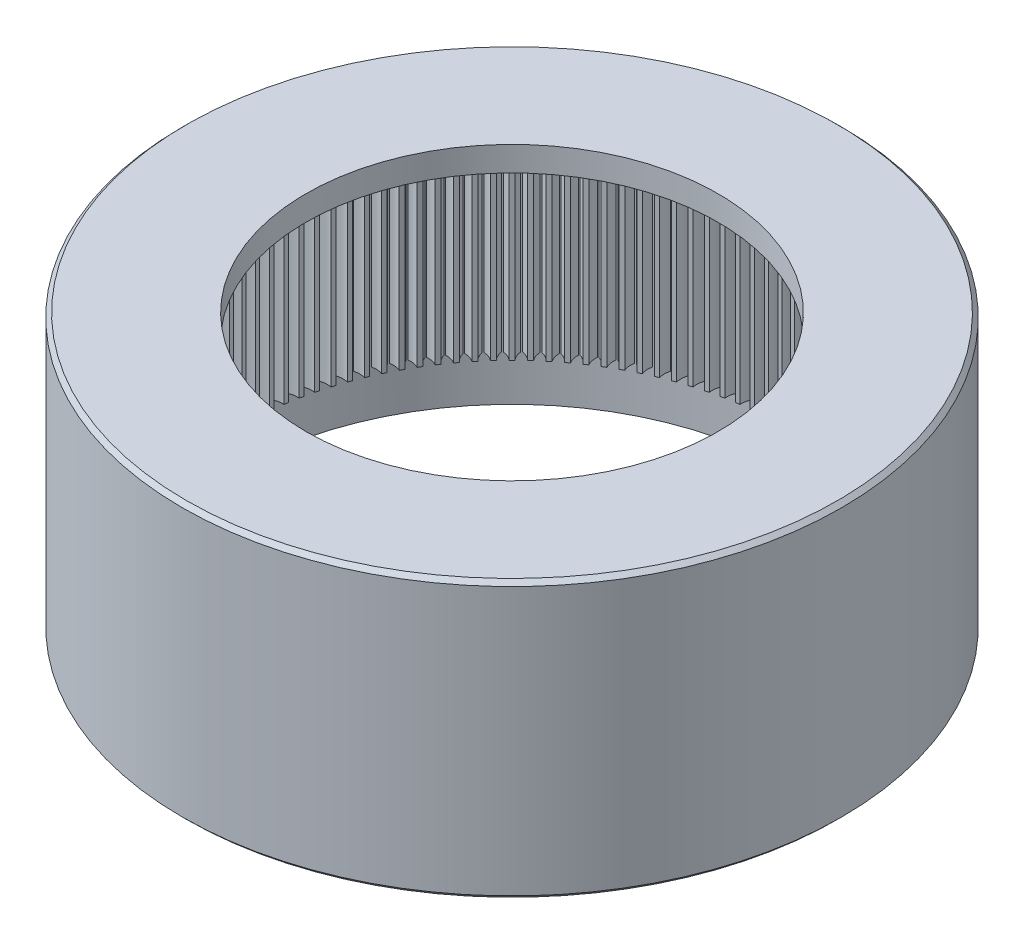
SolidWorks part; units mm, degrees
ref_plane "Front Plane" through (0, 0, 0) normal (0, 0, 1) x (1, 0, 0)
ref_plane "Top Plane" through (0, 0, 0) normal (0, 1, 0) x (1, 0, 0)
ref_plane "Right Plane" through (0, 0, 0) normal (1, 0, 0) x (0, 0, -1)
sketch "Sketch2" plane through (0, 0, 0) normal (0, 1, 0) x (1, 0, 0)
  circle A0 centre (0, 0) radius 75
  circle A1 centre (0, 0) radius 67.5
  dimension "D1" = 150
  dimension "D2" = 135
extrude "Boss-Extrude2" add sketch "Sketch2" along normal blind 51
sketch "Sketch3" plane through (0, 51, 0) normal (0, 1, 0) x (1, 0, 0)
  circle A0 centre (0, 0) radius 67.5 construction
  circle A1 centre (0, 0) radius 67.5
  circle A2 centre (0, 0) radius 65
  dimension "D1" = 130
extrude "Boss-Extrude3" add sketch "Sketch3" against normal blind 44
sketch "Sketch4" plane through (0, 51, 0) normal (0, 1, 0) x (1, 0, 0)
  circle A0 centre (0, 0) radius 67.5
  circle A1 centre (0, 0) radius 65
  dimension "D1" = 135
  dimension "D2" = 130
extrude "Cut-Extrude2" cut sketch "Sketch4" against normal blind 79
sketch "Sketch5" plane through (0, 51, 0) normal (0, 1, 0) x (1, 0, 0)
  line L0 (0, 0) -> (0, 80.4574) construction
  line L1 (-0.5, 64.9981) -> (0.5, 64.9981)
  line L2 (2.6899, 64.9443) -> (3.6887, 64.8953)
  line L3 (5.8733, 64.7341) -> (6.8685, 64.6361)
  line L4 (9.0426, 64.3679) -> (10.0318, 64.2212)
  line L5 (12.1901, 63.8467) -> (13.1709, 63.6516)
  line L6 (15.3082, 63.1717) -> (16.2783, 62.9287)
  line L7 (18.3895, 62.3444) -> (19.3464, 62.0541)
  line L8 (21.4264, 61.367) -> (22.368, 61.0301)
  line L9 (24.4117, 60.2417) -> (25.3356, 59.8591)
  line L10 (27.3383, 58.9713) -> (28.2423, 58.5438)
  line L11 (30.1989, 57.5589) -> (31.0808, 57.0875)
  line L12 (32.9868, 56.0078) -> (33.8446, 55.4937)
  line L13 (35.6953, 54.3217) -> (36.5267, 53.7661)
  line L14 (38.3177, 52.5048) -> (39.1209, 51.9091)
  line L15 (40.8478, 50.5614) -> (41.6208, 49.927)
  line L16 (43.2796, 48.4962) -> (44.0205, 47.8246)
  line L17 (45.607, 46.3141) -> (46.3141, 45.607)
  line L18 (47.8246, 44.0205) -> (48.4962, 43.2796)
  line L19 (49.927, 41.6208) -> (50.5614, 40.8478)
  line L20 (51.9091, 39.1209) -> (52.5048, 38.3177)
  line L21 (53.7661, 36.5267) -> (54.3217, 35.6953)
  line L22 (55.4937, 33.8446) -> (56.0078, 32.9868)
  line L23 (57.0875, 31.0808) -> (57.5589, 30.1989)
  line L24 (58.5438, 28.2423) -> (58.9713, 27.3383)
  line L25 (59.8591, 25.3356) -> (60.2417, 24.4117)
  line L26 (61.0301, 22.368) -> (61.367, 21.4264)
  line L27 (62.0541, 19.3464) -> (62.3444, 18.3895)
  line L28 (62.9287, 16.2783) -> (63.1717, 15.3082)
  line L29 (63.6516, 13.1709) -> (63.8467, 12.1901)
  line L30 (64.2212, 10.0318) -> (64.3679, 9.0426)
  line L31 (64.6361, 6.8685) -> (64.7341, 5.8733)
  line L32 (64.8953, 3.6887) -> (64.9443, 2.6899)
  line L33 (64.9981, 0.5) -> (64.9981, -0.5)
  line L34 (64.9443, -2.6899) -> (64.8953, -3.6887)
  line L35 (64.7341, -5.8733) -> (64.6361, -6.8685)
  line L36 (64.3679, -9.0426) -> (64.2212, -10.0318)
  line L37 (63.8467, -12.1901) -> (63.6516, -13.1709)
  line L38 (63.1717, -15.3082) -> (62.9287, -16.2783)
  line L39 (62.3444, -18.3895) -> (62.0541, -19.3464)
  line L40 (61.367, -21.4264) -> (61.0301, -22.368)
  line L41 (60.2417, -24.4117) -> (59.8591, -25.3356)
  line L42 (58.9713, -27.3383) -> (58.5438, -28.2423)
  line L43 (57.5589, -30.1989) -> (57.0875, -31.0808)
  line L44 (56.0078, -32.9868) -> (55.4937, -33.8446)
  line L45 (54.3217, -35.6953) -> (53.7661, -36.5267)
  line L46 (52.5048, -38.3177) -> (51.9091, -39.1209)
  line L47 (50.5614, -40.8478) -> (49.927, -41.6208)
  line L48 (48.4962, -43.2796) -> (47.8246, -44.0205)
  line L49 (46.3141, -45.607) -> (45.607, -46.3141)
  line L50 (44.0205, -47.8246) -> (43.2796, -48.4962)
  line L51 (41.6208, -49.927) -> (40.8478, -50.5614)
  line L52 (39.1209, -51.9091) -> (38.3177, -52.5048)
  line L53 (36.5267, -53.7661) -> (35.6953, -54.3217)
  line L54 (33.8446, -55.4937) -> (32.9868, -56.0078)
  line L55 (31.0808, -57.0875) -> (30.1989, -57.5589)
  line L56 (28.2423, -58.5438) -> (27.3383, -58.9713)
  line L57 (25.3356, -59.8591) -> (24.4117, -60.2417)
  line L58 (22.368, -61.0301) -> (21.4264, -61.367)
  line L59 (19.3464, -62.0541) -> (18.3895, -62.3444)
  line L60 (16.2783, -62.9287) -> (15.3082, -63.1717)
  line L61 (13.1709, -63.6516) -> (12.1901, -63.8467)
  line L62 (10.0318, -64.2212) -> (9.0426, -64.3679)
  line L63 (6.8685, -64.6361) -> (5.8733, -64.7341)
  line L64 (3.6887, -64.8953) -> (2.6899, -64.9443)
  line L65 (0.5, -64.9981) -> (-0.5, -64.9981)
  line L66 (-2.6899, -64.9443) -> (-3.6887, -64.8953)
  line L67 (-5.8733, -64.7341) -> (-6.8685, -64.6361)
  line L68 (-9.0426, -64.3679) -> (-10.0318, -64.2212)
  line L69 (-12.1901, -63.8467) -> (-13.1709, -63.6516)
  line L70 (-15.3082, -63.1717) -> (-16.2783, -62.9287)
  line L71 (-18.3895, -62.3444) -> (-19.3464, -62.0541)
  line L72 (-21.4264, -61.367) -> (-22.368, -61.0301)
  line L73 (-24.4117, -60.2417) -> (-25.3356, -59.8591)
  line L74 (-27.3383, -58.9713) -> (-28.2423, -58.5438)
  line L75 (-30.1989, -57.5589) -> (-31.0808, -57.0875)
  line L76 (-32.9868, -56.0078) -> (-33.8446, -55.4937)
  line L77 (-35.6953, -54.3217) -> (-36.5267, -53.7661)
  line L78 (-38.3177, -52.5048) -> (-39.1209, -51.9091)
  line L79 (-40.8478, -50.5614) -> (-41.6208, -49.927)
  line L80 (-43.2796, -48.4962) -> (-44.0205, -47.8246)
  line L81 (-45.607, -46.3141) -> (-46.3141, -45.607)
  line L82 (-47.8246, -44.0205) -> (-48.4962, -43.2796)
  line L83 (-49.927, -41.6208) -> (-50.5614, -40.8478)
  line L84 (-51.9091, -39.1209) -> (-52.5048, -38.3177)
  line L85 (-53.7661, -36.5267) -> (-54.3217, -35.6953)
  line L86 (-55.4937, -33.8446) -> (-56.0078, -32.9868)
  line L87 (-57.0875, -31.0808) -> (-57.5589, -30.1989)
  line L88 (-58.5438, -28.2423) -> (-58.9713, -27.3383)
  line L89 (-59.8591, -25.3356) -> (-60.2417, -24.4117)
  line L90 (-61.0301, -22.368) -> (-61.367, -21.4264)
  line L91 (-62.0541, -19.3464) -> (-62.3444, -18.3895)
  line L92 (-62.9287, -16.2783) -> (-63.1717, -15.3082)
  line L93 (-63.6516, -13.1709) -> (-63.8467, -12.1901)
  line L94 (-64.2212, -10.0318) -> (-64.3679, -9.0426)
  line L95 (-64.6361, -6.8685) -> (-64.7341, -5.8733)
  line L96 (-64.8953, -3.6887) -> (-64.9443, -2.6899)
  line L97 (-64.9981, -0.5) -> (-64.9981, 0.5)
  line L98 (-64.9443, 2.6899) -> (-64.8953, 3.6887)
  line L99 (-64.7341, 5.8733) -> (-64.6361, 6.8685)
  line L100 (-64.3679, 9.0426) -> (-64.2212, 10.0318)
  line L101 (-63.8467, 12.1901) -> (-63.6516, 13.1709)
  line L102 (-63.1717, 15.3082) -> (-62.9287, 16.2783)
  line L103 (-62.3444, 18.3895) -> (-62.0541, 19.3464)
  line L104 (-61.367, 21.4264) -> (-61.0301, 22.368)
  line L105 (-60.2417, 24.4117) -> (-59.8591, 25.3356)
  line L106 (-58.9713, 27.3383) -> (-58.5438, 28.2423)
  line L107 (-57.5589, 30.1989) -> (-57.0875, 31.0808)
  line L108 (-56.0078, 32.9868) -> (-55.4937, 33.8446)
  line L109 (-54.3217, 35.6953) -> (-53.7661, 36.5267)
  line L110 (-52.5048, 38.3177) -> (-51.9091, 39.1209)
  line L111 (-50.5614, 40.8478) -> (-49.927, 41.6208)
  line L112 (-48.4962, 43.2796) -> (-47.8246, 44.0205)
  line L113 (-46.3141, 45.607) -> (-45.607, 46.3141)
  line L114 (-44.0205, 47.8246) -> (-43.2796, 48.4962)
  line L115 (-41.6208, 49.927) -> (-40.8478, 50.5614)
  line L116 (-39.1209, 51.9091) -> (-38.3177, 52.5048)
  line L117 (-36.5267, 53.7661) -> (-35.6953, 54.3217)
  line L118 (-33.8446, 55.4937) -> (-32.9868, 56.0078)
  line L119 (-31.0808, 57.0875) -> (-30.1989, 57.5589)
  line L120 (-28.2423, 58.5438) -> (-27.3383, 58.9713)
  line L121 (-25.3356, 59.8591) -> (-24.4117, 60.2417)
  line L122 (-22.368, 61.0301) -> (-21.4264, 61.367)
  line L123 (-19.3464, 62.0541) -> (-18.3895, 62.3444)
  line L124 (-16.2783, 62.9287) -> (-15.3082, 63.1717)
  line L125 (-13.1709, 63.6516) -> (-12.1901, 63.8467)
  line L126 (-10.0318, 64.2212) -> (-9.0426, 64.3679)
  line L127 (-6.8685, 64.6361) -> (-5.8733, 64.7341)
  line L128 (-3.6887, 64.8953) -> (-2.6899, 64.9443)
  circle A0 centre (0, 0) radius 67.5 construction
  circle A1 centre (0, 0) radius 67.5
  circle A2 centre (0, 0) radius 65
  arc A3 (-1.5, 67.4833) -> (-0.5, 64.9981) centre (-4.776, 64.7214) cw
  arc A4 (1.5, 67.4833) -> (0.5, 64.9981) centre (4.776, 64.7214) ccw
  arc A5 (1.8131, 67.4756) -> (2.6899, 64.9443) centre (-1.5945, 64.8777) cw
  arc A6 (4.8094, 67.3284) -> (3.6887, 64.8953) centre (7.9459, 64.4091) ccw
  arc A7 (5.1217, 67.3054) -> (5.8733, 64.7341) centre (1.5908, 64.8778) cw
  arc A8 (8.1073, 67.0114) -> (6.8685, 64.6361) centre (11.0968, 63.9416) ccw
  arc A9 (8.4181, 66.973) -> (9.0426, 64.3679) centre (4.7723, 64.7216) cw
  arc A10 (11.3856, 66.5328) -> (10.0318, 64.2212) centre (14.2209, 63.3201) ccw
  arc A11 (11.6942, 66.4793) -> (12.1901, 63.8467) centre (7.9423, 64.4095) cw
  arc A12 (14.6365, 65.894) -> (13.1709, 63.6516) centre (17.3107, 62.546) ccw
  arc A13 (14.9421, 65.8254) -> (15.3082, 63.1717) centre (11.0932, 63.9422) cw
  arc A14 (17.8522, 65.0965) -> (16.2783, 62.9287) centre (20.3588, 61.6213) ccw
  arc A15 (18.154, 65.0129) -> (18.3895, 62.3444) centre (14.2173, 63.3209) cw
  arc A16 (21.0248, 64.1421) -> (19.3464, 62.0541) centre (23.3579, 60.5481) ccw
  arc A17 (21.3221, 64.0439) -> (21.4264, 61.367) centre (17.3072, 62.547) cw
  arc A18 (24.1468, 63.0332) -> (22.368, 61.0301) centre (26.3007, 59.329) ccw
  arc A19 (24.4389, 62.9205) -> (24.4117, 60.2417) centre (20.3554, 61.6224) cw
  arc A20 (27.2106, 61.7724) -> (25.3356, 59.8591) centre (29.1802, 57.9671) ccw
  arc A21 (27.4969, 61.6455) -> (27.3383, 58.9713) centre (23.3545, 60.5494) cw
  arc A22 (30.2088, 60.3629) -> (28.2423, 58.5438) centre (31.9894, 56.4654) ccw
  arc A23 (30.4885, 60.2221) -> (30.1989, 57.5589) centre (26.2974, 59.3305) cw
  arc A24 (33.1343, 58.8079) -> (31.0808, 57.0875) centre (34.7215, 54.8278) ccw
  arc A25 (33.4068, 58.6535) -> (32.9868, 56.0078) centre (29.1769, 57.9687) cw
  arc A26 (35.98, 57.1112) -> (33.8446, 55.4937) centre (37.3699, 53.058) ccw
  arc A27 (36.2445, 56.9437) -> (35.6953, 54.3217) centre (31.9862, 56.4672) cw
  arc A28 (38.7389, 55.277) -> (36.5267, 53.7661) centre (39.9283, 51.1605) ccw
  arc A29 (38.995, 55.0967) -> (38.3177, 52.5048) centre (34.7184, 54.8297) cw
  arc A30 (41.4046, 53.3096) -> (39.1209, 51.9091) centre (42.3906, 49.1396) ccw
  arc A31 (41.6515, 53.1169) -> (40.8478, 50.5614) centre (37.3669, 53.0601) cw
  arc A32 (43.9705, 51.2137) -> (41.6208, 49.927) centre (44.7507, 47.0004) ccw
  arc A33 (44.2076, 51.0092) -> (43.2796, 48.4962) centre (39.9255, 51.1627) cw
  arc A34 (46.4305, 48.9945) -> (44.0205, 47.8246) centre (47.003, 44.748) ccw
  arc A35 (46.6573, 48.7786) -> (45.607, 46.3141) centre (42.3878, 49.142) cw
  arc A36 (48.7786, 46.6573) -> (46.3141, 45.607) centre (49.142, 42.3878) ccw
  arc A37 (48.9945, 46.4305) -> (47.8246, 44.0205) centre (44.748, 47.003) cw
  arc A38 (51.0092, 44.2076) -> (48.4962, 43.2796) centre (51.1627, 39.9255) ccw
  arc A39 (51.2137, 43.9705) -> (49.927, 41.6208) centre (47.0004, 44.7507) cw
  arc A40 (53.1169, 41.6515) -> (50.5614, 40.8478) centre (53.0601, 37.3669) ccw
  arc A41 (53.3096, 41.4046) -> (51.9091, 39.1209) centre (49.1396, 42.3906) cw
  arc A42 (55.0967, 38.995) -> (52.5048, 38.3177) centre (54.8297, 34.7184) ccw
  arc A43 (55.277, 38.7389) -> (53.7661, 36.5267) centre (51.1605, 39.9283) cw
  arc A44 (56.9437, 36.2445) -> (54.3217, 35.6953) centre (56.4672, 31.9862) ccw
  arc A45 (57.1112, 35.98) -> (55.4937, 33.8446) centre (53.058, 37.3699) cw
  arc A46 (58.6535, 33.4068) -> (56.0078, 32.9868) centre (57.9687, 29.1769) ccw
  arc A47 (58.8079, 33.1343) -> (57.0875, 31.0808) centre (54.8278, 34.7215) cw
  arc A48 (60.2221, 30.4885) -> (57.5589, 30.1989) centre (59.3305, 26.2974) ccw
  arc A49 (60.3629, 30.2088) -> (58.5438, 28.2423) centre (56.4654, 31.9894) cw
  arc A50 (61.6455, 27.4969) -> (58.9713, 27.3383) centre (60.5494, 23.3545) ccw
  arc A51 (61.7724, 27.2106) -> (59.8591, 25.3356) centre (57.9671, 29.1802) cw
  arc A52 (62.9205, 24.4389) -> (60.2417, 24.4117) centre (61.6224, 20.3554) ccw
  arc A53 (63.0332, 24.1468) -> (61.0301, 22.368) centre (59.329, 26.3007) cw
  arc A54 (64.0439, 21.3221) -> (61.367, 21.4264) centre (62.547, 17.3072) ccw
  arc A55 (64.1421, 21.0248) -> (62.0541, 19.3464) centre (60.5481, 23.3579) cw
  arc A56 (65.0129, 18.154) -> (62.3444, 18.3895) centre (63.3209, 14.2173) ccw
  arc A57 (65.0965, 17.8522) -> (62.9287, 16.2783) centre (61.6213, 20.3588) cw
  arc A58 (65.8254, 14.9421) -> (63.1717, 15.3082) centre (63.9422, 11.0932) ccw
  arc A59 (65.894, 14.6365) -> (63.6516, 13.1709) centre (62.546, 17.3107) cw
  arc A60 (66.4793, 11.6942) -> (63.8467, 12.1901) centre (64.4095, 7.9423) ccw
  arc A61 (66.5328, 11.3856) -> (64.2212, 10.0318) centre (63.3201, 14.2209) cw
  arc A62 (66.973, 8.4181) -> (64.3679, 9.0426) centre (64.7216, 4.7723) ccw
  arc A63 (67.0114, 8.1073) -> (64.6361, 6.8685) centre (63.9416, 11.0968) cw
  arc A64 (67.3054, 5.1217) -> (64.7341, 5.8733) centre (64.8778, 1.5908) ccw
  arc A65 (67.3284, 4.8094) -> (64.8953, 3.6887) centre (64.4091, 7.9459) cw
  arc A66 (67.4756, 1.8131) -> (64.9443, 2.6899) centre (64.8777, -1.5945) ccw
  arc A67 (67.4833, 1.5) -> (64.9981, 0.5) centre (64.7214, 4.776) cw
  arc A68 (67.4833, -1.5) -> (64.9981, -0.5) centre (64.7214, -4.776) ccw
  arc A69 (67.4756, -1.8131) -> (64.9443, -2.6899) centre (64.8777, 1.5945) cw
  arc A70 (67.3284, -4.8094) -> (64.8953, -3.6887) centre (64.4091, -7.9459) ccw
  arc A71 (67.3054, -5.1217) -> (64.7341, -5.8733) centre (64.8778, -1.5908) cw
  arc A72 (67.0114, -8.1073) -> (64.6361, -6.8685) centre (63.9416, -11.0968) ccw
  arc A73 (66.973, -8.4181) -> (64.3679, -9.0426) centre (64.7216, -4.7723) cw
  arc A74 (66.5328, -11.3856) -> (64.2212, -10.0318) centre (63.3201, -14.2209) ccw
  arc A75 (66.4793, -11.6942) -> (63.8467, -12.1901) centre (64.4095, -7.9423) cw
  arc A76 (65.894, -14.6365) -> (63.6516, -13.1709) centre (62.546, -17.3107) ccw
  arc A77 (65.8254, -14.9421) -> (63.1717, -15.3082) centre (63.9422, -11.0932) cw
  arc A78 (65.0965, -17.8522) -> (62.9287, -16.2783) centre (61.6213, -20.3588) ccw
  arc A79 (65.0129, -18.154) -> (62.3444, -18.3895) centre (63.3209, -14.2173) cw
  arc A80 (64.1421, -21.0248) -> (62.0541, -19.3464) centre (60.5481, -23.3579) ccw
  arc A81 (64.0439, -21.3221) -> (61.367, -21.4264) centre (62.547, -17.3072) cw
  arc A82 (63.0332, -24.1468) -> (61.0301, -22.368) centre (59.329, -26.3007) ccw
  arc A83 (62.9205, -24.4389) -> (60.2417, -24.4117) centre (61.6224, -20.3554) cw
  arc A84 (61.7724, -27.2106) -> (59.8591, -25.3356) centre (57.9671, -29.1802) ccw
  arc A85 (61.6455, -27.4969) -> (58.9713, -27.3383) centre (60.5494, -23.3545) cw
  arc A86 (60.3629, -30.2088) -> (58.5438, -28.2423) centre (56.4654, -31.9894) ccw
  arc A87 (60.2221, -30.4885) -> (57.5589, -30.1989) centre (59.3305, -26.2974) cw
  arc A88 (58.8079, -33.1343) -> (57.0875, -31.0808) centre (54.8278, -34.7215) ccw
  arc A89 (58.6535, -33.4068) -> (56.0078, -32.9868) centre (57.9687, -29.1769) cw
  arc A90 (57.1112, -35.98) -> (55.4937, -33.8446) centre (53.058, -37.3699) ccw
  arc A91 (56.9437, -36.2445) -> (54.3217, -35.6953) centre (56.4672, -31.9862) cw
  arc A92 (55.277, -38.7389) -> (53.7661, -36.5267) centre (51.1605, -39.9283) ccw
  arc A93 (55.0967, -38.995) -> (52.5048, -38.3177) centre (54.8297, -34.7184) cw
  arc A94 (53.3096, -41.4046) -> (51.9091, -39.1209) centre (49.1396, -42.3906) ccw
  arc A95 (53.1169, -41.6515) -> (50.5614, -40.8478) centre (53.0601, -37.3669) cw
  arc A96 (51.2137, -43.9705) -> (49.927, -41.6208) centre (47.0004, -44.7507) ccw
  arc A97 (51.0092, -44.2076) -> (48.4962, -43.2796) centre (51.1627, -39.9255) cw
  arc A98 (48.9945, -46.4305) -> (47.8246, -44.0205) centre (44.748, -47.003) ccw
  arc A99 (48.7786, -46.6573) -> (46.3141, -45.607) centre (49.142, -42.3878) cw
  arc A100 (46.6573, -48.7786) -> (45.607, -46.3141) centre (42.3878, -49.142) ccw
  arc A101 (46.4305, -48.9945) -> (44.0205, -47.8246) centre (47.003, -44.748) cw
  arc A102 (44.2076, -51.0092) -> (43.2796, -48.4962) centre (39.9255, -51.1627) ccw
  arc A103 (43.9705, -51.2137) -> (41.6208, -49.927) centre (44.7507, -47.0004) cw
  arc A104 (41.6515, -53.1169) -> (40.8478, -50.5614) centre (37.3669, -53.0601) ccw
  arc A105 (41.4046, -53.3096) -> (39.1209, -51.9091) centre (42.3906, -49.1396) cw
  arc A106 (38.995, -55.0967) -> (38.3177, -52.5048) centre (34.7184, -54.8297) ccw
  arc A107 (38.7389, -55.277) -> (36.5267, -53.7661) centre (39.9283, -51.1605) cw
  arc A108 (36.2445, -56.9437) -> (35.6953, -54.3217) centre (31.9862, -56.4672) ccw
  arc A109 (35.98, -57.1112) -> (33.8446, -55.4937) centre (37.3699, -53.058) cw
  arc A110 (33.4068, -58.6535) -> (32.9868, -56.0078) centre (29.1769, -57.9687) ccw
  arc A111 (33.1343, -58.8079) -> (31.0808, -57.0875) centre (34.7215, -54.8278) cw
  arc A112 (30.4885, -60.2221) -> (30.1989, -57.5589) centre (26.2974, -59.3305) ccw
  arc A113 (30.2088, -60.3629) -> (28.2423, -58.5438) centre (31.9894, -56.4654) cw
  arc A114 (27.4969, -61.6455) -> (27.3383, -58.9713) centre (23.3545, -60.5494) ccw
  arc A115 (27.2106, -61.7724) -> (25.3356, -59.8591) centre (29.1802, -57.9671) cw
  arc A116 (24.4389, -62.9205) -> (24.4117, -60.2417) centre (20.3554, -61.6224) ccw
  arc A117 (24.1468, -63.0332) -> (22.368, -61.0301) centre (26.3007, -59.329) cw
  arc A118 (21.3221, -64.0439) -> (21.4264, -61.367) centre (17.3072, -62.547) ccw
  arc A119 (21.0248, -64.1421) -> (19.3464, -62.0541) centre (23.3579, -60.5481) cw
  arc A120 (18.154, -65.0129) -> (18.3895, -62.3444) centre (14.2173, -63.3209) ccw
  arc A121 (17.8522, -65.0965) -> (16.2783, -62.9287) centre (20.3588, -61.6213) cw
  arc A122 (14.9421, -65.8254) -> (15.3082, -63.1717) centre (11.0932, -63.9422) ccw
  arc A123 (14.6365, -65.894) -> (13.1709, -63.6516) centre (17.3107, -62.546) cw
  arc A124 (11.6942, -66.4793) -> (12.1901, -63.8467) centre (7.9423, -64.4095) ccw
  arc A125 (11.3856, -66.5328) -> (10.0318, -64.2212) centre (14.2209, -63.3201) cw
  arc A126 (8.4181, -66.973) -> (9.0426, -64.3679) centre (4.7723, -64.7216) ccw
  arc A127 (8.1073, -67.0114) -> (6.8685, -64.6361) centre (11.0968, -63.9416) cw
  arc A128 (5.1217, -67.3054) -> (5.8733, -64.7341) centre (1.5908, -64.8778) ccw
  arc A129 (4.8094, -67.3284) -> (3.6887, -64.8953) centre (7.9459, -64.4091) cw
  arc A130 (1.8131, -67.4756) -> (2.6899, -64.9443) centre (-1.5945, -64.8777) ccw
  arc A131 (1.5, -67.4833) -> (0.5, -64.9981) centre (4.776, -64.7214) cw
  arc A132 (-1.5, -67.4833) -> (-0.5, -64.9981) centre (-4.776, -64.7214) ccw
  arc A133 (-1.8131, -67.4756) -> (-2.6899, -64.9443) centre (1.5945, -64.8777) cw
  arc A134 (-4.8094, -67.3284) -> (-3.6887, -64.8953) centre (-7.9459, -64.4091) ccw
  arc A135 (-5.1217, -67.3054) -> (-5.8733, -64.7341) centre (-1.5908, -64.8778) cw
  arc A136 (-8.1073, -67.0114) -> (-6.8685, -64.6361) centre (-11.0968, -63.9416) ccw
  arc A137 (-8.4181, -66.973) -> (-9.0426, -64.3679) centre (-4.7723, -64.7216) cw
  arc A138 (-11.3856, -66.5328) -> (-10.0318, -64.2212) centre (-14.2209, -63.3201) ccw
  arc A139 (-11.6942, -66.4793) -> (-12.1901, -63.8467) centre (-7.9423, -64.4095) cw
  arc A140 (-14.6365, -65.894) -> (-13.1709, -63.6516) centre (-17.3107, -62.546) ccw
  arc A141 (-14.9421, -65.8254) -> (-15.3082, -63.1717) centre (-11.0932, -63.9422) cw
  arc A142 (-17.8522, -65.0965) -> (-16.2783, -62.9287) centre (-20.3588, -61.6213) ccw
  arc A143 (-18.154, -65.0129) -> (-18.3895, -62.3444) centre (-14.2173, -63.3209) cw
  arc A144 (-21.0248, -64.1421) -> (-19.3464, -62.0541) centre (-23.3579, -60.5481) ccw
  arc A145 (-21.3221, -64.0439) -> (-21.4264, -61.367) centre (-17.3072, -62.547) cw
  arc A146 (-24.1468, -63.0332) -> (-22.368, -61.0301) centre (-26.3007, -59.329) ccw
  arc A147 (-24.4389, -62.9205) -> (-24.4117, -60.2417) centre (-20.3554, -61.6224) cw
  arc A148 (-27.2106, -61.7724) -> (-25.3356, -59.8591) centre (-29.1802, -57.9671) ccw
  arc A149 (-27.4969, -61.6455) -> (-27.3383, -58.9713) centre (-23.3545, -60.5494) cw
  arc A150 (-30.2088, -60.3629) -> (-28.2423, -58.5438) centre (-31.9894, -56.4654) ccw
  arc A151 (-30.4885, -60.2221) -> (-30.1989, -57.5589) centre (-26.2974, -59.3305) cw
  arc A152 (-33.1343, -58.8079) -> (-31.0808, -57.0875) centre (-34.7215, -54.8278) ccw
  arc A153 (-33.4068, -58.6535) -> (-32.9868, -56.0078) centre (-29.1769, -57.9687) cw
  arc A154 (-35.98, -57.1112) -> (-33.8446, -55.4937) centre (-37.3699, -53.058) ccw
  arc A155 (-36.2445, -56.9437) -> (-35.6953, -54.3217) centre (-31.9862, -56.4672) cw
  arc A156 (-38.7389, -55.277) -> (-36.5267, -53.7661) centre (-39.9283, -51.1605) ccw
  arc A157 (-38.995, -55.0967) -> (-38.3177, -52.5048) centre (-34.7184, -54.8297) cw
  arc A158 (-41.4046, -53.3096) -> (-39.1209, -51.9091) centre (-42.3906, -49.1396) ccw
  arc A159 (-41.6515, -53.1169) -> (-40.8478, -50.5614) centre (-37.3669, -53.0601) cw
  arc A160 (-43.9705, -51.2137) -> (-41.6208, -49.927) centre (-44.7507, -47.0004) ccw
  arc A161 (-44.2076, -51.0092) -> (-43.2796, -48.4962) centre (-39.9255, -51.1627) cw
  arc A162 (-46.4305, -48.9945) -> (-44.0205, -47.8246) centre (-47.003, -44.748) ccw
  arc A163 (-46.6573, -48.7786) -> (-45.607, -46.3141) centre (-42.3878, -49.142) cw
  arc A164 (-48.7786, -46.6573) -> (-46.3141, -45.607) centre (-49.142, -42.3878) ccw
  arc A165 (-48.9945, -46.4305) -> (-47.8246, -44.0205) centre (-44.748, -47.003) cw
  arc A166 (-51.0092, -44.2076) -> (-48.4962, -43.2796) centre (-51.1627, -39.9255) ccw
  arc A167 (-51.2137, -43.9705) -> (-49.927, -41.6208) centre (-47.0004, -44.7507) cw
  arc A168 (-53.1169, -41.6515) -> (-50.5614, -40.8478) centre (-53.0601, -37.3669) ccw
  arc A169 (-53.3096, -41.4046) -> (-51.9091, -39.1209) centre (-49.1396, -42.3906) cw
  arc A170 (-55.0967, -38.995) -> (-52.5048, -38.3177) centre (-54.8297, -34.7184) ccw
  arc A171 (-55.277, -38.7389) -> (-53.7661, -36.5267) centre (-51.1605, -39.9283) cw
  arc A172 (-56.9437, -36.2445) -> (-54.3217, -35.6953) centre (-56.4672, -31.9862) ccw
  arc A173 (-57.1112, -35.98) -> (-55.4937, -33.8446) centre (-53.058, -37.3699) cw
  arc A174 (-58.6535, -33.4068) -> (-56.0078, -32.9868) centre (-57.9687, -29.1769) ccw
  arc A175 (-58.8079, -33.1343) -> (-57.0875, -31.0808) centre (-54.8278, -34.7215) cw
  arc A176 (-60.2221, -30.4885) -> (-57.5589, -30.1989) centre (-59.3305, -26.2974) ccw
  arc A177 (-60.3629, -30.2088) -> (-58.5438, -28.2423) centre (-56.4654, -31.9894) cw
  arc A178 (-61.6455, -27.4969) -> (-58.9713, -27.3383) centre (-60.5494, -23.3545) ccw
  arc A179 (-61.7724, -27.2106) -> (-59.8591, -25.3356) centre (-57.9671, -29.1802) cw
  arc A180 (-62.9205, -24.4389) -> (-60.2417, -24.4117) centre (-61.6224, -20.3554) ccw
  arc A181 (-63.0332, -24.1468) -> (-61.0301, -22.368) centre (-59.329, -26.3007) cw
  arc A182 (-64.0439, -21.3221) -> (-61.367, -21.4264) centre (-62.547, -17.3072) ccw
  arc A183 (-64.1421, -21.0248) -> (-62.0541, -19.3464) centre (-60.5481, -23.3579) cw
  arc A184 (-65.0129, -18.154) -> (-62.3444, -18.3895) centre (-63.3209, -14.2173) ccw
  arc A185 (-65.0965, -17.8522) -> (-62.9287, -16.2783) centre (-61.6213, -20.3588) cw
  arc A186 (-65.8254, -14.9421) -> (-63.1717, -15.3082) centre (-63.9422, -11.0932) ccw
  arc A187 (-65.894, -14.6365) -> (-63.6516, -13.1709) centre (-62.546, -17.3107) cw
  arc A188 (-66.4793, -11.6942) -> (-63.8467, -12.1901) centre (-64.4095, -7.9423) ccw
  arc A189 (-66.5328, -11.3856) -> (-64.2212, -10.0318) centre (-63.3201, -14.2209) cw
  arc A190 (-66.973, -8.4181) -> (-64.3679, -9.0426) centre (-64.7216, -4.7723) ccw
  arc A191 (-67.0114, -8.1073) -> (-64.6361, -6.8685) centre (-63.9416, -11.0968) cw
  arc A192 (-67.3054, -5.1217) -> (-64.7341, -5.8733) centre (-64.8778, -1.5908) ccw
  arc A193 (-67.3284, -4.8094) -> (-64.8953, -3.6887) centre (-64.4091, -7.9459) cw
  arc A194 (-67.4756, -1.8131) -> (-64.9443, -2.6899) centre (-64.8777, 1.5945) ccw
  arc A195 (-67.4833, -1.5) -> (-64.9981, -0.5) centre (-64.7214, -4.776) cw
  arc A196 (-67.4833, 1.5) -> (-64.9981, 0.5) centre (-64.7214, 4.776) ccw
  arc A197 (-67.4756, 1.8131) -> (-64.9443, 2.6899) centre (-64.8777, -1.5945) cw
  arc A198 (-67.3284, 4.8094) -> (-64.8953, 3.6887) centre (-64.4091, 7.9459) ccw
  arc A199 (-67.3054, 5.1217) -> (-64.7341, 5.8733) centre (-64.8778, 1.5908) cw
  arc A200 (-67.0114, 8.1073) -> (-64.6361, 6.8685) centre (-63.9416, 11.0968) ccw
  arc A201 (-66.973, 8.4181) -> (-64.3679, 9.0426) centre (-64.7216, 4.7723) cw
  arc A202 (-66.5328, 11.3856) -> (-64.2212, 10.0318) centre (-63.3201, 14.2209) ccw
  arc A203 (-66.4793, 11.6942) -> (-63.8467, 12.1901) centre (-64.4095, 7.9423) cw
  arc A204 (-65.894, 14.6365) -> (-63.6516, 13.1709) centre (-62.546, 17.3107) ccw
  arc A205 (-65.8254, 14.9421) -> (-63.1717, 15.3082) centre (-63.9422, 11.0932) cw
  arc A206 (-65.0965, 17.8522) -> (-62.9287, 16.2783) centre (-61.6213, 20.3588) ccw
  arc A207 (-65.0129, 18.154) -> (-62.3444, 18.3895) centre (-63.3209, 14.2173) cw
  arc A208 (-64.1421, 21.0248) -> (-62.0541, 19.3464) centre (-60.5481, 23.3579) ccw
  arc A209 (-64.0439, 21.3221) -> (-61.367, 21.4264) centre (-62.547, 17.3072) cw
  arc A210 (-63.0332, 24.1468) -> (-61.0301, 22.368) centre (-59.329, 26.3007) ccw
  arc A211 (-62.9205, 24.4389) -> (-60.2417, 24.4117) centre (-61.6224, 20.3554) cw
  arc A212 (-61.7724, 27.2106) -> (-59.8591, 25.3356) centre (-57.9671, 29.1802) ccw
  arc A213 (-61.6455, 27.4969) -> (-58.9713, 27.3383) centre (-60.5494, 23.3545) cw
  arc A214 (-60.3629, 30.2088) -> (-58.5438, 28.2423) centre (-56.4654, 31.9894) ccw
  arc A215 (-60.2221, 30.4885) -> (-57.5589, 30.1989) centre (-59.3305, 26.2974) cw
  arc A216 (-58.8079, 33.1343) -> (-57.0875, 31.0808) centre (-54.8278, 34.7215) ccw
  arc A217 (-58.6535, 33.4068) -> (-56.0078, 32.9868) centre (-57.9687, 29.1769) cw
  arc A218 (-57.1112, 35.98) -> (-55.4937, 33.8446) centre (-53.058, 37.3699) ccw
  arc A219 (-56.9437, 36.2445) -> (-54.3217, 35.6953) centre (-56.4672, 31.9862) cw
  arc A220 (-55.277, 38.7389) -> (-53.7661, 36.5267) centre (-51.1605, 39.9283) ccw
  arc A221 (-55.0967, 38.995) -> (-52.5048, 38.3177) centre (-54.8297, 34.7184) cw
  arc A222 (-53.3096, 41.4046) -> (-51.9091, 39.1209) centre (-49.1396, 42.3906) ccw
  arc A223 (-53.1169, 41.6515) -> (-50.5614, 40.8478) centre (-53.0601, 37.3669) cw
  arc A224 (-51.2137, 43.9705) -> (-49.927, 41.6208) centre (-47.0004, 44.7507) ccw
  arc A225 (-51.0092, 44.2076) -> (-48.4962, 43.2796) centre (-51.1627, 39.9255) cw
  arc A226 (-48.9945, 46.4305) -> (-47.8246, 44.0205) centre (-44.748, 47.003) ccw
  arc A227 (-48.7786, 46.6573) -> (-46.3141, 45.607) centre (-49.142, 42.3878) cw
  arc A228 (-46.6573, 48.7786) -> (-45.607, 46.3141) centre (-42.3878, 49.142) ccw
  arc A229 (-46.4305, 48.9945) -> (-44.0205, 47.8246) centre (-47.003, 44.748) cw
  arc A230 (-44.2076, 51.0092) -> (-43.2796, 48.4962) centre (-39.9255, 51.1627) ccw
  arc A231 (-43.9705, 51.2137) -> (-41.6208, 49.927) centre (-44.7507, 47.0004) cw
  arc A232 (-41.6515, 53.1169) -> (-40.8478, 50.5614) centre (-37.3669, 53.0601) ccw
  arc A233 (-41.4046, 53.3096) -> (-39.1209, 51.9091) centre (-42.3906, 49.1396) cw
  arc A234 (-38.995, 55.0967) -> (-38.3177, 52.5048) centre (-34.7184, 54.8297) ccw
  arc A235 (-38.7389, 55.277) -> (-36.5267, 53.7661) centre (-39.9283, 51.1605) cw
  arc A236 (-36.2445, 56.9437) -> (-35.6953, 54.3217) centre (-31.9862, 56.4672) ccw
  arc A237 (-35.98, 57.1112) -> (-33.8446, 55.4937) centre (-37.3699, 53.058) cw
  arc A238 (-33.4068, 58.6535) -> (-32.9868, 56.0078) centre (-29.1769, 57.9687) ccw
  arc A239 (-33.1343, 58.8079) -> (-31.0808, 57.0875) centre (-34.7215, 54.8278) cw
  arc A240 (-30.4885, 60.2221) -> (-30.1989, 57.5589) centre (-26.2974, 59.3305) ccw
  arc A241 (-30.2088, 60.3629) -> (-28.2423, 58.5438) centre (-31.9894, 56.4654) cw
  arc A242 (-27.4969, 61.6455) -> (-27.3383, 58.9713) centre (-23.3545, 60.5494) ccw
  arc A243 (-27.2106, 61.7724) -> (-25.3356, 59.8591) centre (-29.1802, 57.9671) cw
  arc A244 (-24.4389, 62.9205) -> (-24.4117, 60.2417) centre (-20.3554, 61.6224) ccw
  arc A245 (-24.1468, 63.0332) -> (-22.368, 61.0301) centre (-26.3007, 59.329) cw
  arc A246 (-21.3221, 64.0439) -> (-21.4264, 61.367) centre (-17.3072, 62.547) ccw
  arc A247 (-21.0248, 64.1421) -> (-19.3464, 62.0541) centre (-23.3579, 60.5481) cw
  arc A248 (-18.154, 65.0129) -> (-18.3895, 62.3444) centre (-14.2173, 63.3209) ccw
  arc A249 (-17.8522, 65.0965) -> (-16.2783, 62.9287) centre (-20.3588, 61.6213) cw
  arc A250 (-14.9421, 65.8254) -> (-15.3082, 63.1717) centre (-11.0932, 63.9422) ccw
  arc A251 (-14.6365, 65.894) -> (-13.1709, 63.6516) centre (-17.3107, 62.546) cw
  arc A252 (-11.6942, 66.4793) -> (-12.1901, 63.8467) centre (-7.9423, 64.4095) ccw
  arc A253 (-11.3856, 66.5328) -> (-10.0318, 64.2212) centre (-14.2209, 63.3201) cw
  arc A254 (-8.4181, 66.973) -> (-9.0426, 64.3679) centre (-4.7723, 64.7216) ccw
  arc A255 (-8.1073, 67.0114) -> (-6.8685, 64.6361) centre (-11.0968, 63.9416) cw
  arc A256 (-5.1217, 67.3054) -> (-5.8733, 64.7341) centre (-1.5908, 64.8778) ccw
  arc A257 (-4.8094, 67.3284) -> (-3.6887, 64.8953) centre (-7.9459, 64.4091) cw
  arc A258 (-1.8131, 67.4756) -> (-2.6899, 64.9443) centre (1.5945, 64.8777) ccw
  point P776 (0, 0)
  circle M4 centre (0, 0) radius 67.5
  dimension "D1" = 130
  dimension "D2" = 0.5
  dimension "D3" = 1.5
  dimension "D4" = 128
extrude "Boss-Extrude4" add sketch "Sketch5" against normal blind 40 contours A258 A257 A2 M4 | A256 A255 A2 M4 | A2 L0 A3 M4 | L0 A2 A4 A1 | A6 A5 A2 M4 | A8 A7 A2 M4 | A10 A9 A2 M4 | A12 A11 A2 M4 | A14 A13 A2 M4 | A16 A15 A2 M4 | A18 A17 A2 M4 | A20 A19 A2 M4 | A22 A21 A2 M4 | A24 A23 A2 M4 | A26 A25 A2 M4 | A28 A27 A2 M4 | A30 A29 A2 M4 | A32 A31 A2 M4 | A34 A33 A2 M4 | A38 A37 A2 M4 | A40 A39 A2 M4 | A42 A41 A2 M4 | A44 A43 A2 M4 | A46 A45 A2 M4 | A48 A47 A2 M4 | A50 A49 A2 M4 | A54 A53 A2 M4 | A56 A55 A2 M4 | A36 A35 A2 M4 | A52 A51 A2 M4 | A58 A57 A2 M4 | A60 A59 A2 M4 | A62 A61 A2 M4 | A64 A63 A2 M4 | A66 A65 A2 M4 | A68 A67 A2 M4 | A70 A69 A2 M4 | A72 A71 A2 M4 | A74 A73 A2 M4 | A76 A75 A2 M4 | A78 A77 A2 M4 | A80 A79 A2 M4 | A82 A81 A2 M4 | A84 A83 A2 M4 | A86 A85 A2 M4 | A88 A87 A2 M4 | A90 A89 A2 M4 | A92 A91 A2 M4 | A94 A93 A2 M4 | A96 A95 A2 M4 | A98 A97 A2 M4 | A100 A99 A2 M4 | A102 A101 A2 M4 | A104 A103 A2 M4 | A106 A105 A2 M4 | A108 A107 A2 M4 | A110 A109 A2 M4 | A112 A111 A2 M4 | A114 A113 A2 M4 | A116 A115 A2 M4 | A118 A117 A2 M4 | A120 A119 A2 M4 | A122 A121 A2 M4 | A124 A123 A2 M4 | A126 A125 A2 M4 | A128 A127 A2 M4 | A130 A129 A2 M4 | A132 A131 A2 M4 | A134 A133 A2 M4 | A136 A135 A2 M4 | A138 A137 A2 M4 | A140 A139 A2 M4 | A142 A141 A2 M4 | A144 A143 A2 M4 | A146 A145 A2 M4 | A148 A147 A2 M4 | A150 A149 A2 M4 | A152 A151 A2 M4 | A154 A153 A2 M4 | A156 A155 A2 M4 | A158 A157 A2 M4 | A160 A159 A2 M4 | A162 A161 A2 M4 | A164 A163 A2 M4 | A166 A165 A2 M4 | A168 A167 A2 M4 | A170 A169 A2 M4 | A172 A171 A2 M4 | A174 A173 A2 M4 | A176 A175 A2 M4 | A178 A177 A2 M4 | A254 A253 A2 M4 | A252 A251 A2 M4 | A250 A249 A2 M4 | A248 A247 A2 M4 | A246 A245 A2 M4 | A244 A243 A2 M4 | A242 A241 A2 M4 | A240 A239 A2 M4 | A238 A237 A2 M4 | A236 A235 A2 M4 | A234 A233 A2 M4 | A232 A231 A2 M4 | A230 A229 A2 M4 | A228 A227 A2 M4 | A226 A225 A2 M4 | A224 A223 A2 M4 | A222 A221 A2 M4 | A220 A219 A2 M4 | A218 A217 A2 M4 | A216 A215 A2 M4 | A214 A213 A2 M4 | A212 A211 A2 M4 | A210 A209 A2 M4 | A208 A207 A2 M4 | A206 A205 A2 M4 | A204 A203 A2 M4 | A202 A201 A2 M4 | A200 A199 A2 M4 | A198 A197 A2 M4 | A196 A195 A2 M4 | A194 A193 A2 M4 | A192 A191 A2 M4 | A190 A189 A2 M4 | A188 A187 A2 M4 | A186 A185 A2 M4 | A184 A183 A2 M4 | A182 A181 A2 M4 | A180 A179 A2 M4
chamfer "Chamfer1" distance 0.5 angle 45 1 edges at (0, 51, 75)
chamfer "Chamfer2" distance 0.5 angle 45 1 edges at (0, 0, 75)
sketch "Sketch7" plane through (0, 0, 0) normal (0, -1, 0) x (1, 0, 0)
  line L0 (0, 0) -> (0, 93.519) construction
  line L1 (0, 74.05) -> (0, 67)
  circle A0 centre (0, 0) radius 75
  circle A2 centre (0, 0) radius 67
  arc A3 (-6.1, 66.7217) -> (0, 74.05) centre (-0.2501, 68.0552) cw
  circle A4 centre (0, 0) radius 74.5
  arc A7 (6.1, 66.7217) -> (0, 74.05) centre (0.2501, 68.0552) ccw
  arc A8 (66.7217, 6.1) -> (74.05, 0) centre (68.0552, 0.2501) cw
  arc A9 (66.7217, -6.1) -> (74.05, 0) centre (68.0552, -0.2501) ccw
  arc A10 (6.1, -66.7217) -> (0, -74.05) centre (0.2501, -68.0552) cw
  arc A11 (-6.1, -66.7217) -> (0, -74.05) centre (-0.2501, -68.0552) ccw
  arc A12 (-66.7217, -6.1) -> (-74.05, 0) centre (-68.0552, -0.2501) cw
  arc A13 (-66.7217, 6.1) -> (-74.05, 0) centre (-68.0552, 0.2501) ccw
  arc A14 (-8.2, 66.4963) -> (-6.1663, 69.0545) centre (-11.7022, 71.3681) ccw
  arc A15 (8.2, 66.4963) -> (6.1663, 69.0545) centre (11.7022, 71.3681) cw
  arc A16 (66.4963, 8.2) -> (69.0545, 6.1663) centre (71.3681, 11.7022) ccw
  arc A17 (66.4963, -8.2) -> (69.0545, -6.1663) centre (71.3681, -11.7022) cw
  arc A18 (8.2, -66.4963) -> (6.1663, -69.0545) centre (11.7022, -71.3681) ccw
  arc A19 (-8.2, -66.4963) -> (-6.1663, -69.0545) centre (-11.7022, -71.3681) cw
  arc A20 (-66.4963, -8.2) -> (-69.0545, -6.1663) centre (-71.3681, -11.7022) ccw
  arc A21 (-66.4963, 8.2) -> (-69.0545, 6.1663) centre (-71.3681, 11.7022) cw
  point P30 (0, 0)
  point P55 (0, 0)
  circle M8 centre (0, 0) radius 67.5
  dimension "D1" = 150
  dimension "D2" = 134
  dimension "D3" = 6
  dimension "D5" = 7.05
  dimension "D6" = 149
  dimension "D7" = 4
  dimension "D9" = 6
  dimension "D4" = 6.1
  dimension "D8" = 2.1
  dimension "D10" = 4
extrude "Cut-Extrude3" cut sketch "Sketch7" against normal blind 3 contours A3 L1 M8 | A7 L1 M8 | A14 A3 M8 | A15 A7 M8 | A9 A8 M8 | A17 A9 M8 | A16 A8 M8 | A11 A10 M8 | A19 A11 M8 | A18 A10 M8 | A13 A12 M8 | A20 A12 M8 | A21 A13 M8
sketch "Sketch9" plane through (0, 51, 0) normal (0, 1, 0) x (1, 0, 0)
  circle A0 centre (0, 0) radius 74.5
  circle A1 centre (0, 0) radius 80
  dimension "D1" = 149
  dimension "D2" = 160
extrude "Boss-Extrude7" add sketch "Sketch9" against normal blind 51
sketch "Sketch10" plane through (0, 0, 0) normal (0, -1, 0) x (1, 0, 0)
  line L0 (0, 0) -> (0, 112.3554) construction
  line L1 (0, 67.5) -> (0, 76.5)
  circle A0 centre (0, 0) radius 75
  circle A1 centre (0, 0) radius 67.5
  arc A2 (-8, 67.0242) -> (0, 76.5) centre (0.9844, 67.554) cw
  arc A3 (-10.9702, 66.6026) -> (-7.4633, 70.6582) centre (-19.6107, 77.6181) ccw
  arc A4 (8, 67.0242) -> (0, 76.5) centre (-0.9844, 67.554) ccw
  arc A5 (10.9702, 66.6026) -> (7.4633, 70.6582) centre (19.6107, 77.6181) cw
  arc A6 (67.0242, 8) -> (76.5, 0) centre (67.554, -0.9844) cw
  arc A7 (66.6026, 10.9702) -> (70.6582, 7.4633) centre (77.6181, 19.6107) ccw
  arc A8 (67.0242, -8) -> (76.5, 0) centre (67.554, 0.9844) ccw
  arc A9 (66.6026, -10.9702) -> (70.6582, -7.4633) centre (77.6181, -19.6107) cw
  arc A10 (8, -67.0242) -> (0, -76.5) centre (-0.9844, -67.554) cw
  arc A11 (10.9702, -66.6026) -> (7.4633, -70.6582) centre (19.6107, -77.6181) ccw
  arc A12 (-8, -67.0242) -> (0, -76.5) centre (0.9844, -67.554) ccw
  arc A13 (-10.9702, -66.6026) -> (-7.4633, -70.6582) centre (-19.6107, -77.6181) cw
  arc A14 (-67.0242, -8) -> (-76.5, 0) centre (-67.554, 0.9844) cw
  arc A15 (-66.6026, -10.9702) -> (-70.6582, -7.4633) centre (-77.6181, -19.6107) ccw
  arc A16 (-67.0242, 8) -> (-76.5, 0) centre (-67.554, -0.9844) ccw
  arc A17 (-66.6026, 10.9702) -> (-70.6582, 7.4633) centre (-77.6181, 19.6107) cw
  point P53 (0, 0)
  arc M5 (0, 74.05) -> (6.1663, 69.0545) centre (0.2501, 68.0552) cw
  arc M6 (6.1663, 69.0545) -> (7.5039, 67.0816) centre (11.7022, 71.3681) ccw
  arc M7 (7.5039, 67.0816) -> (67.0816, 7.5039) centre (0, 0) cw
  arc M8 (67.0816, 7.5039) -> (69.0545, 6.1663) centre (71.3681, 11.7022) ccw
  arc M9 (69.0545, 6.1663) -> (74.05, 0) centre (68.0552, 0.2501) cw
  arc M10 (74.05, 0) -> (69.0545, -6.1663) centre (68.0552, -0.2501) cw
  arc M11 (69.0545, -6.1663) -> (67.0816, -7.5039) centre (71.3681, -11.7022) ccw
  arc M12 (67.0816, -7.5039) -> (7.5039, -67.0816) centre (0, 0) cw
  arc M13 (7.5039, -67.0816) -> (6.1663, -69.0545) centre (11.7022, -71.3681) ccw
  arc M14 (6.1663, -69.0545) -> (0, -74.05) centre (0.2501, -68.0552) cw
  arc M15 (0, -74.05) -> (-6.1663, -69.0545) centre (-0.2501, -68.0552) cw
  arc M16 (-6.1663, -69.0545) -> (-7.5039, -67.0816) centre (-11.7022, -71.3681) ccw
  arc M17 (-7.5039, -67.0816) -> (-67.0816, -7.5039) centre (0, 0) cw
  arc M18 (-67.0816, -7.5039) -> (-69.0545, -6.1663) centre (-71.3681, -11.7022) ccw
  arc M19 (-69.0545, -6.1663) -> (-74.05, 0) centre (-68.0552, -0.2501) cw
  arc M20 (-74.05, 0) -> (-69.0545, 6.1663) centre (-68.0552, 0.2501) cw
  arc M21 (-69.0545, 6.1663) -> (-67.0816, 7.5039) centre (-71.3681, 11.7022) ccw
  arc M22 (-67.0816, 7.5039) -> (-7.5039, 67.0816) centre (0, 0) cw
  arc M23 (-7.5039, 67.0816) -> (-6.1663, 69.0545) centre (-11.7022, 71.3681) ccw
  arc M24 (-6.1663, 69.0545) -> (0, 74.05) centre (-0.2501, 68.0552) cw
  dimension "D1" = 150
  dimension "D2" = 135
  dimension "D4" = 9
  dimension "D7" = 14
  dimension "D3" = 9
  dimension "D5" = 8
  dimension "D6" = 3
  dimension "D8" = 4
extrude "Cut-Extrude4" cut sketch "Sketch10" against normal blind 3 contours A3 A1 A2 | A2 A1 L1 A0 M23 M24 | A2 A0 L1 | A0 A4 L1 | A4 A0 L1 M7 M5 M6 | A1 A5 A4 | A0 A8 A6 | A8 A0 A6 A1 M12 M8 M9 M10 M11 | A7 A1 A6 | A1 A9 A8 | A12 A0 A10 A1 M17 M13 M14 M15 M16 | A1 A13 A12 | A11 A1 A10 | A0 A12 A10 | A1 A17 A16 | A16 A0 A14 A1 M22 M18 M19 M20 M21 | A0 A16 A14 | A15 A1 A14
sketch "Sketch11" plane through (0, 0, 0) normal (0, -1, 0) x (1, 0, 0)
  circle A1 centre (0, 71.25) radius 3.2
  circle A2 centre (71.25, 0) radius 3.2
  circle A3 centre (0, -71.25) radius 3.2
  circle A4 centre (-71.25, 0) radius 3.2
  point P12 (0, 0)
  dimension "D1" = 4
  dimension "D2" = 6.4
extrude "Cut-Extrude5" cut sketch "Sketch11" against normal blind 10
chamfer "Chamfer6" distance 1 angle 45 1 edges at (0, 0, 80)
sketch "Sketch12" plane through (0, 0, 0) normal (0, -1, 0) x (1, 0, 0)
  circle A1 centre (51.2652, 51.2652) radius 3.2
  circle A2 centre (51.2652, -51.2652) radius 3.2
  circle A3 centre (-51.2652, -51.2652) radius 3.2
  circle A4 centre (-51.2652, 51.2652) radius 3.2
  point P14 (0, 0)
  dimension "D2" = 6.4
  dimension "D3" = 4
extrude "Cut-Extrude6" cut sketch "Sketch12" against normal blind 10
sketch "Sketch13" plane through (0, 51, 0) normal (0, 1, 0) x (1, 0, 0)
  circle A0 centre (0, 0) radius 80
  circle A1 centre (0, 0) radius 67.5
  dimension "D1" = 135
extrude "Boss-Extrude8" add sketch "Sketch13" along normal blind 9
sketch "Sketch14" plane through (0, 60, 0) normal (0, 1, 0) x (1, 0, 0)
  circle A0 centre (0, 0) radius 80
  circle A1 centre (0, 0) radius 50
  dimension "D1" = 100
extrude "Boss-Extrude9" add sketch "Sketch14" along normal blind 5
sketch "Sketch15" plane through (0, 65, 0) normal (0, 1, 0) x (1, 0, 0)
  circle A1 centre (0, 0) radius 67.5
  dimension "D1" = 135
extrude "Cut-Extrude9" cut sketch "Sketch15" against normal blind 5
sketch "Sketch16" plane through (0, 65, 0) normal (0, 1, 0) x (1, 0, 0)
  circle A0 centre (0, 0) radius 80
  circle A1 centre (0, 0) radius 67.5
  dimension "D1" = 160
  dimension "D2" = 135
extrude "Boss-Extrude10" add sketch "Sketch16" along normal blind 2
sketch "Sketch17" plane through (0, 67, 0) normal (0, 1, 0) x (1, 0, 0)
  circle A0 centre (0, 0) radius 80
  circle A1 centre (0, 0) radius 50
  dimension "D1" = 100
extrude "Boss-Extrude11" add sketch "Sketch17" against normal blind 6
chamfer "Chamfer8" distance 1 angle 45 1 edges at (0, 67, 80)
